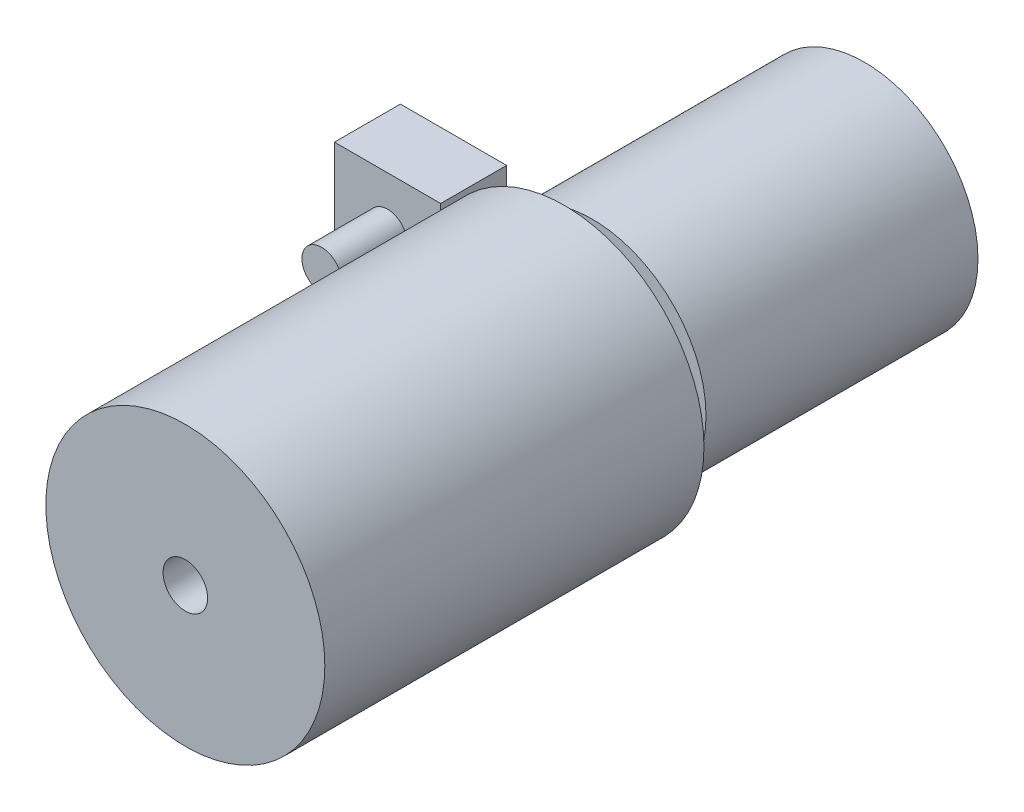
SolidWorks part; units mm, degrees
ref_plane "Front Plane" through (0, 0, 0) normal (0, 0, 1) x (1, 0, 0)
ref_plane "Top Plane" through (0, 0, 0) normal (0, 1, 0) x (1, 0, 0)
ref_plane "Right Plane" through (0, 0, 0) normal (1, 0, 0) x (0, 0, -1)
sketch "Sketch2" plane through (0, 0, 0) normal (0, 0, 1) x (1, 0, 0)
  circle A0 centre (0, 0) radius 13.7713
extrude "Boss-Extrude1" add sketch "Sketch2" along normal blind 33
sketch "Sketch4" plane through (0, 0, 33) normal (0, 0, 1) x (1, 0, 0)
  circle A0 centre (0, 0) radius 2.6705
extrude "Boss-Extrude2" add sketch "Sketch4" along normal blind 3.4012
sketch "Sketch5" plane through (0, 0, 33) normal (0, 0, 1) x (1, 0, 0)
  line L0 (0, 0) -> (-24.8647, 0)
  circle A0 centre (-24.8647, 0) radius 2.3918
extrude "Boss-Extrude3" add sketch "Sketch5" along normal blind 8 separate body
sketch "Sketch6" plane through (0, 0, 33) normal (0, 0, -1) x (-1, 0, 0)
  line L1 (18.4224, -6.2138) -> (31.3071, -6.2138)
  line L2 (18.4224, -6.2138) -> (18.4224, 6.2138)
  line L3 (18.4224, 6.2138) -> (31.3071, 6.2138)
  line L4 (31.3071, -6.2138) -> (31.3071, 6.2138)
  line L5 (18.4224, -6.2138) -> (31.3071, 6.2138) construction
  line L6 (18.4224, 6.2138) -> (31.3071, -6.2138) construction
  point P0 (24.8647, 0)
extrude "Boss-Extrude4" add sketch "Sketch6" along normal blind 8
sketch "Sketch20" plane through (0, 0, 36.4012) normal (0, 0, 1) x (1, 0, 0)
sketch "Sketch23" plane through (0, 0, 41) normal (0, 0, 1) x (1, 0, 0)
  circle A0 centre (-24.8647, 0) radius 2.426
sketch "Sketch24" plane through (0, 0, 36.4012) normal (0, 0, 1) x (1, 0, 0)
  circle A0 centre (0, 0) radius 2.7046
  circle A1 centre (0, 0) radius 16.9246
extrude "Boss-Extrude9" add sketch "Sketch24" along normal blind 46 separate body contours A0 | A1
